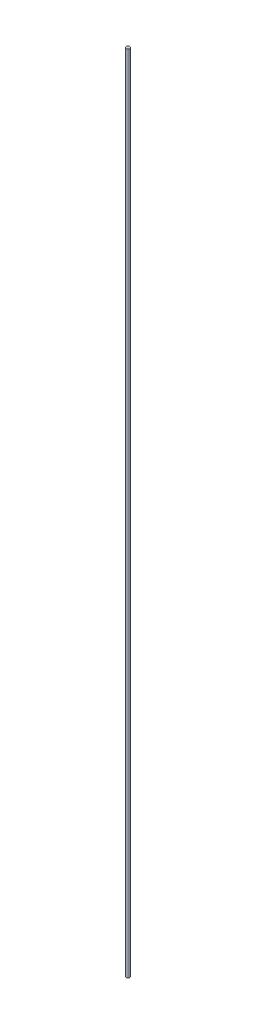
SolidWorks part; units mm, degrees
ref_plane "Front Plane" through (0, 0, 0) normal (0, 0, 1) x (1, 0, 0)
ref_plane "Top Plane" through (0, 0, 0) normal (0, 1, 0) x (1, 0, 0)
ref_plane "Right Plane" through (0, 0, 0) normal (1, 0, 0) x (0, 0, -1)
sketch "Sketch1" plane through (0, 0, 0) normal (0, 1, 0) x (1, 0, 0)
  circle A0 centre (0, 0) radius 0.45
  dimension "D1" = 0.9
extrude "Boss-Extrude1" add sketch "Sketch1" along normal blind 200
